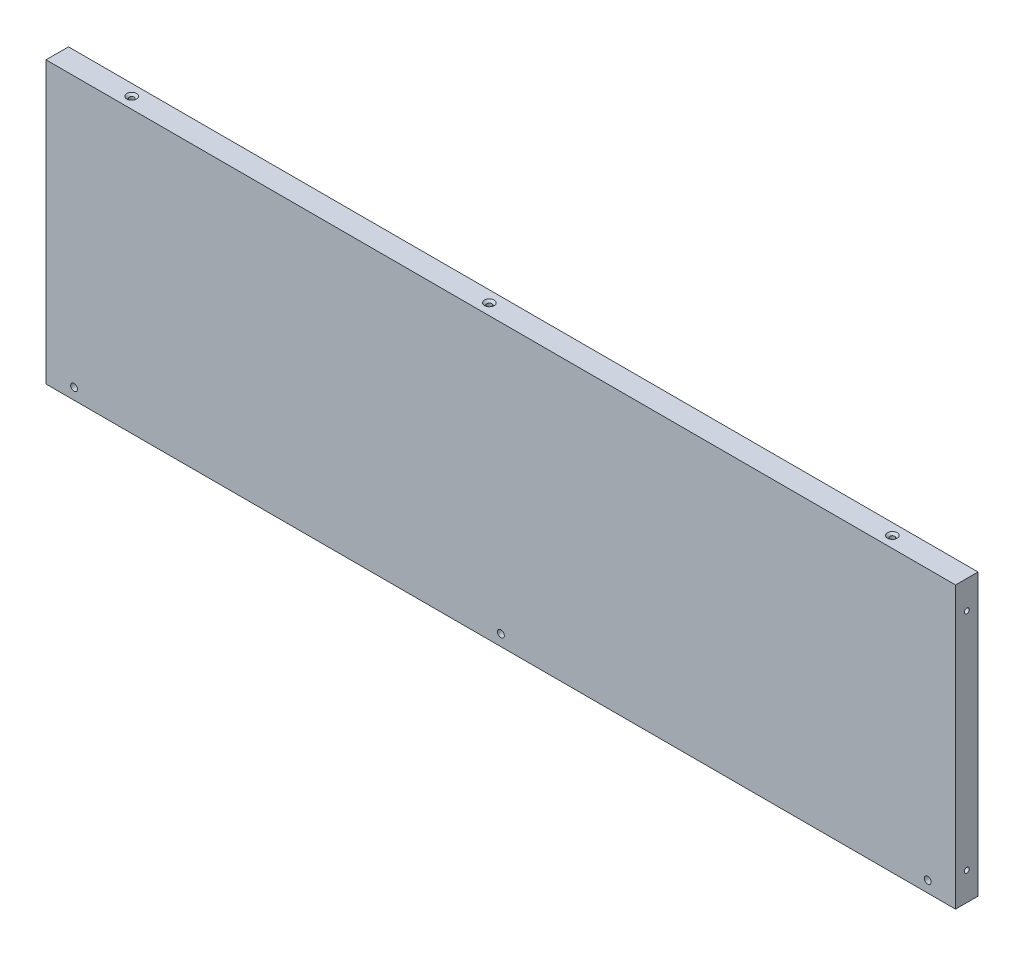
SolidWorks part; units mm, degrees
ref_plane "Front Plane" through (0, 0, 0) normal (0, 0, 1) x (1, 0, 0)
ref_plane "Top Plane" through (0, 0, 0) normal (0, 1, 0) x (1, 0, 0)
ref_plane "Right Plane" through (0, 0, 0) normal (1, 0, 0) x (0, 0, -1)
sketch "Sketch1" plane through (0, 0, 0) normal (0, 0, 1) x (1, 0, 0)
  line L1 (0, 0) -> (324, 0)
  line L2 (0, 0) -> (0, 100)
  line L3 (0, 100) -> (324, 100)
  line L4 (324, 0) -> (324, 100)
  dimension "D1" = 100
  dimension "D2" = 324
extrude "Boss-Extrude1" add sketch "Sketch1" along normal blind 8
hole_wizard "CBORE for #2 Socket Head Cap Screw1" positions "Sketch2" profile "Sketch3" counterbore size "#2" standard "ANSI Inch" end condition through all
sketch "Sketch2" plane through (0, 0, 0) normal (0, 0, -1) x (-1, 0, 0)
  line L0 (-306, 100) -> (-306, 0)
  line L1 (-324, 100) -> (0, 100) construction
  line L2 (0, 0) -> (-324, 0) construction
  line L5 (-8, 100) -> (-8, 0)
  point P2 (-314, 4)
  point P4 (-10, 4)
  point P27 (-162, 4)
  point P32 (-162, 0)
  dimension "D1" = 152
  dimension "D2" = 152
  dimension "D3" = 4
  dimension "D4" = 4
  dimension "D7" = 0
  dimension "D8" = 4
sketch "Sketch3" plane through (314, 4, 0) normal (1, 0, 0) x (0, 1, 0)
  line L0 (0, 0) -> (0, 8)
  line L1 (0, 8) -> (1.2192, 8)
  line L3 (1.2192, 8) -> (1.2192, 2.1844)
  line L4 (1.2192, 2.1844) -> (2.3812, 2.1844)
  line L5 (2.3812, 2.1844) -> (2.3812, 0)
  line L7 (2.3812, 0) -> (0, 0)
  line L11 (0, -6.35) -> (0, 107.95) construction
  dimension "Thru Hole Dia." = 2.4384
  dimension "Thru Hole Depth" = 8
  dimension "C'Bore Dia." = 4.7625
  dimension "C'Bore Depth" = 2.1844
hole_wizard "#2-56 Tapped Hole1" positions "Sketch7" profile "Sketch6" tap size "#2-56" standard "ANSI Inch"
sketch "Sketch7" plane through (324, 0, 0) normal (1, 0, 0) x (0, 0, -1)
  line L0 (-8, 100) -> (0, 100) construction
  line L1 (-8, 0) -> (0, 0) construction
  point P0 (-4, 90)
  point P2 (-4, 10)
  dimension "D1" = 10
  dimension "D2" = 10
sketch "Sketch6" plane through (324, 90, 4) normal (0, 1, 0) x (0, 0, -1)
  line L0 (0, 0) -> (0, 15.5342)
  line L1 (0, 15.5342) -> (0.889, 15)
  line L2 (0.889, 15) -> (0.889, 0)
  line L5 (0.889, 0) -> (0, 0)
  line L10 (0, 15.5342) -> (-0.889, 15) construction
  line L11 (0, -6.35) -> (0, 107.95) construction
  dimension "Tap Drill Dia." = 1.778
  dimension "Tap Drill Depth" = 15
  dimension "Drill Angle" = 118
cosmetic thread "Hole Thread1" parameters "D1"=12, "D2"=2.1844
cosmetic thread "Hole Thread2" parameters "D1"=12, "D2"=2.1844
hole_wizard "#2-56 Tapped Hole2" positions "Sketch8" profile "Sketch9" tap size "#2-56" standard "ANSI Inch"
sketch "Sketch8" plane through (0, 0, 0) normal (-1, 0, 0) x (0, 0, 1)
  line L0 (8, 100) -> (0, 100) construction
  line L2 (8, 0) -> (0, 0) construction
  point P0 (4, 90)
  point P2 (4, 10)
  dimension "D1" = 10
  dimension "D2" = 10
sketch "Sketch9" plane through (0, 90, 4) normal (0, 1, 0) x (0, 0, 1)
  line L0 (0, 0) -> (0, 15.5342)
  line L1 (0, 15.5342) -> (0.889, 15)
  line L2 (0.889, 15) -> (0.889, 0)
  line L5 (0.889, 0) -> (0, 0)
  line L10 (0, 15.5342) -> (-0.889, 15) construction
  line L11 (0, -6.35) -> (0, 107.95) construction
  dimension "Tap Drill Dia." = 1.778
  dimension "Tap Drill Depth" = 15
  dimension "Drill Angle" = 118
cosmetic thread "Hole Thread3" parameters "D1"=12, "D2"=2.1844
cosmetic thread "Hole Thread4" parameters "D1"=12, "D2"=2.1844
sketch "Sketch10" plane through (324, 0, 0) normal (1, 0, 0) x (0, 0, -1)
  line L1 (-8, 100) -> (0, 100)
  line L2 (-8, 100) -> (-8, 0)
  line L3 (-8, 0) -> (0, 0)
  line L4 (0, 100) -> (0, 0)
extrude "Cut-Extrude1" cut sketch "Sketch10" against normal blind 0.1
sketch "Sketch11" plane through (0, 0, 0) normal (-1, 0, 0) x (0, 0, 1)
  line L1 (0, 100) -> (8, 100)
  line L2 (0, 100) -> (0, 0)
  line L3 (0, 0) -> (8, 0)
  line L4 (8, 100) -> (8, 0)
sketch "Sketch12" plane through (0, 100, 0) normal (0, 1, 0) x (1, 0, 0)
  line L0 (323.9, 0) -> (0, 0) construction
  line L1 (0, 0) -> (0, -8) construction
  line L2 (323.9, 0) -> (323.9, -8) construction
  point P0 (26.5, -4)
  point P5 (153.9, -4)
  point P8 (297.4, -4)
  dimension "D1" = 4
  dimension "D2" = 26.5
  dimension "D3" = 170
  dimension "D4" = 4
  dimension "D5" = 4
  dimension "D6" = 26.5
hole_wizard "#2-56 Tapped Hole3" positions "Sketch17" profile "Sketch19" tap size "#2-56" standard "ANSI Inch"
sketch "Sketch17" plane through (0, 100, 0) normal (0, 1, 0) x (1, 0, 0)
  point P0 (297.4, -4)
  point P3 (153.9, -4)
  point P6 (26.5, -4)
sketch "Sketch19" plane through (297.4, 100, 4) normal (1, 0, 0) x (0, 0, 1)
  line L0 (0, 0) -> (0, 6.2642)
  line L1 (0, 6.2642) -> (0.889, 5.73)
  line L2 (0.889, 5.73) -> (0.889, 0.7033)
  line L3 (0.889, 0.7033) -> (1.7272, 0)
  line L5 (1.7272, 0) -> (0, 0)
  line L6 (-0.889, 0.7033) -> (-1.7272, 0) construction
  line L10 (0, 6.2642) -> (-0.889, 5.73) construction
  line L11 (0, -6.35) -> (0, 107.95) construction
  dimension "Tap Drill Dia." = 1.778
  dimension "Tap Drill Depth" = 5.73
  dimension "Near C'Sink Dia." = 3.4544
  dimension "Near C'Sink Angle" = 100
  dimension "Drill Angle" = 118
cosmetic thread "Hole Thread5" parameters "D1"=4.37, "D2"=2.1844
cosmetic thread "Hole Thread6" parameters "D1"=4.37, "D2"=2.1844
cosmetic thread "Hole Thread7" parameters "D1"=4.37, "D2"=2.1844
